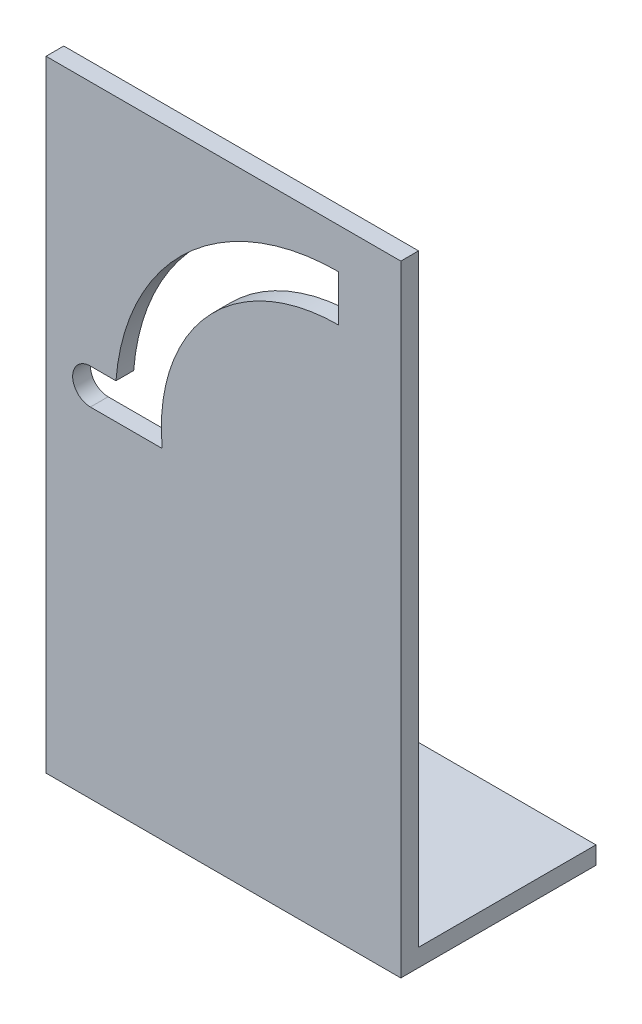
SolidWorks part; units mm, degrees
ref_plane "前视基准面" through (0, 0, 0) normal (0, 0, 1) x (1, 0, 0)
ref_plane "上视基准面" through (0, 0, 0) normal (0, 1, 0) x (1, 0, 0)
ref_plane "右视基准面" through (0, 0, 0) normal (1, 0, 0) x (0, 0, -1)
sketch "草图1" plane through (0, 0, 0) normal (0, 0, 1) x (1, 0, 0)
  line L0 (-30.2714, 30.2806) -> (-30.2714, -39.7194)
  line L1 (-30.2714, -39.7194) -> (9.7286, -39.7194)
  line L2 (9.7286, -39.7194) -> (9.7286, 30.2806)
  line L3 (9.7286, 30.2806) -> (-30.2714, 30.2806)
  line L4 (-30.2714, -39.7194) -> (-25.2714, -39.7194) construction
  line L5 (-25.2714, -39.7194) -> (-25.2714, 0.5306) construction
  line L6 (-25.2714, -1.4694) -> (-21.2714, -1.4694)
  line L7 (-25.2714, 2.5306) -> (-22.392, 2.5306)
  line L8 (-21.2714, 0.5306) -> (-21.2714, -1.4694) construction
  line L9 (-21.2714, 0.5306) -> (2.7286, 0.5306) construction
  line L10 (-21.2714, -1.4694) -> (-17.1712, -1.4694)
  line L11 (2.7286, 20.5306) -> (2.7286, 25.7306)
  arc A0 (-25.2714, 2.5306) -> (-25.2714, -1.4694) centre (-25.2714, 0.5306) ccw
  arc A1 (2.7286, 25.7306) -> (-22.392, 2.5306) centre (2.7286, 0.5306) ccw
  arc A2 (2.7286, 20.5306) -> (-17.1712, -1.4694) centre (2.7286, 0.5306) ccw
  dimension "D5" = 4
  dimension "D8" = 40
  dimension "D1" = 70
  dimension "D2" = 40
  dimension "D3" = 5
  dimension "D4" = 40.25
  dimension "D6" = 4
  dimension "D7" = 24
extrude "凸台-拉伸1" add sketch "草图1" along normal blind 2
sketch "草图2" plane through (0, 0, 2) normal (0, 0, 1) x (1, 0, 0)
  line L0 (-30.2714, -39.7194) -> (-30.2714, -37.7194)
  line L1 (-30.2714, 30.2806) -> (-30.2714, -39.7194) construction
  line L2 (-30.2714, -37.7194) -> (9.7286, -37.7194)
  line L3 (9.7286, -39.7194) -> (9.7286, 30.2806) construction
  line L4 (9.7286, -37.7194) -> (9.7286, -39.7194)
  line L5 (9.7286, -39.7194) -> (-30.2714, -39.7194)
  dimension "D1" = 2
extrude "凸台-拉伸2" add sketch "草图2" against normal blind 22
